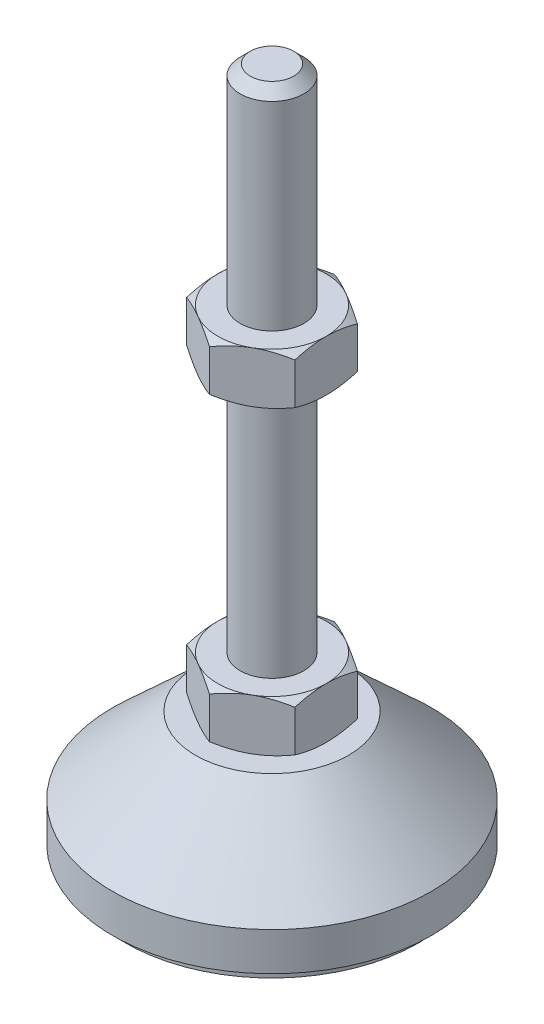
SolidWorks part; units mm, degrees
ref_plane "Спереди" through (0, 0, 0) normal (0, 0, 1) x (1, 0, 0)
ref_plane "Сверху" through (0, 0, 0) normal (0, 1, 0) x (1, 0, 0)
ref_plane "Справа" through (0, 0, 0) normal (1, 0, 0) x (0, 0, -1)
sketch "Эскиз1" plane through (0, 0, 0) normal (0, 0, 1) x (1, 0, 0)
  line L0 (0, 0) -> (-23, 0)
  line L1 (-23, 0) -> (-23, 2)
  line L2 (-23, 2) -> (-25, 2)
  line L3 (-25, 2) -> (-25, 8)
  line L4 (-25, 8) -> (-12, 20)
  line L5 (-12, 20) -> (-5, 20)
  line L12 (-5, 28) -> (-5, 106.4)
  line L13 (-5, 106.4) -> (-3.4, 108)
  line L14 (-3.4, 108) -> (0, 108)
  line L15 (0, 108) -> (0, 0) construction
  line L16 (-5, 20) -> (0, 20) construction
  line L17 (0, 0) -> (0, 108)
  line L18 (0, 0) -> (0, -7.9595) construction
  line L19 (-5, 28) -> (-5, 20)
  point P8 (-5, 67.2)
  point P23 (-8.5, 20)
  dimension "D1" = 10
  dimension "D2" = 20
  dimension "D3" = 8
  dimension "D4" = 50
  dimension "D5" = 5
  dimension "D6" = 1.6
  dimension "D7" = 45
  dimension "D8" = 24
  dimension "D9" = 2
  dimension "D10" = 80
  dimension "D11" = 6
revolve "Повернуть1" add sketch "Эскиз1" angle 360 about L17
sketch "Эскиз2" plane through (0, 20, 0) normal (0, 1, 0) x (1, 0, 0)
  line L1 (0, 9.815) -> (-8.5, 4.9075)
  line L2 (-8.5, 4.9075) -> (-8.5, -4.9075)
  line L3 (-8.5, -4.9075) -> (0, -9.815)
  line L4 (0, -9.815) -> (8.5, -4.9075)
  line L5 (8.5, -4.9075) -> (8.5, 4.9075)
  line L6 (8.5, 4.9075) -> (0, 9.815)
  circle A0 centre (0, 0) radius 8.5 construction
  dimension "D1" = 17
extrude "Бобышка-Вытянуть1" add sketch "Эскиз2" along normal up to vertex (8 mm away) up to point (-5, 28, 0)
ref_plane "Плоскость1" through (0, 67.2, 0) normal (0, 1, 0) x (1, 0, 0)
sketch "Эскиз3" plane through (0, 67.2, 0) normal (0, 1, 0) x (1, 0, 0)
  line L6 (8.5, 4.9075) -> (0, 9.815)
  line L7 (0, 9.815) -> (-8.5, 4.9075)
  line L8 (-8.5, 4.9075) -> (-8.5, -4.9075)
  line L9 (-8.5, -4.9075) -> (0, -9.815)
  line L10 (0, -9.815) -> (8.5, -4.9075)
  line L11 (8.5, -4.9075) -> (8.5, 4.9075)
  line L12 (8.5, 4.9075) -> (0, 9.815)
  line L13 (0, 9.815) -> (-8.5, 4.9075)
  line L14 (-8.5, 4.9075) -> (-8.5, -4.9075)
  line L15 (-8.5, -4.9075) -> (0, -9.815)
  line L16 (0, -9.815) -> (8.5, -4.9075)
  line L17 (8.5, -4.9075) -> (8.5, 4.9075)
  dimension "D1" = 0
extrude "Бобышка-Вытянуть2" add sketch "Эскиз3" along normal blind 8
sketch "Эскиз4" plane through (0, 0, 0) normal (0, 0, 1) x (1, 0, 0)
  line L0 (-8.5, 75.2) -> (-15.4282, 71.2)
  line L1 (-15.4282, 71.2) -> (-15.4282, 75.2)
  line L2 (-15.4282, 75.2) -> (-8.5, 75.2)
  line L3 (-15.4282, 71.2) -> (-8.5, 67.2)
  line L4 (50, 67.2) -> (-50, 67.2) construction
  line L5 (-8.5, 67.2) -> (-15.4282, 67.2)
  line L6 (-15.4282, 67.2) -> (-15.4282, 71.2)
  line L7 (-8.5, 75.2) -> (-8.5, 67.2) construction
  line L8 (-8.5, 28) -> (-15.4282, 28)
  line L9 (-15.4282, 28) -> (-15.4282, 24)
  line L10 (-15.4282, 24) -> (-8.5, 28)
  line L11 (-8.5, 20) -> (-15.4282, 24)
  line L12 (-15.4282, 24) -> (-15.4282, 20)
  line L13 (-15.4282, 20) -> (-8.5, 20)
  line L14 (0, 108) -> (0, 96.3793) construction
  dimension "D1" = 30
  dimension "D2" = 30
revolve "Вырез-Повернуть2" cut sketch "Эскиз4" angle 360 about L14
